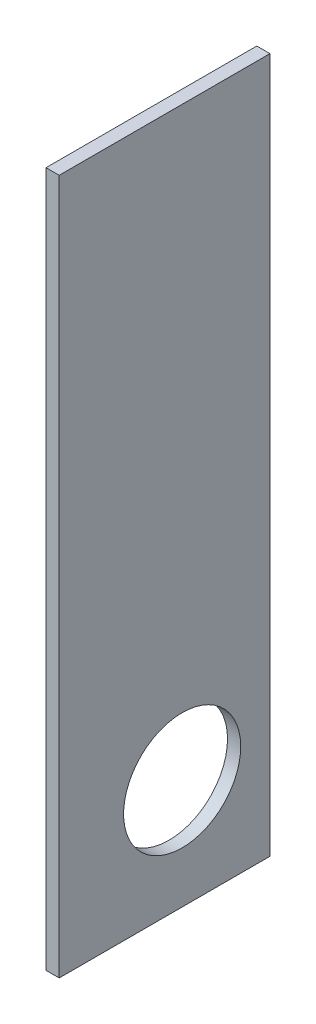
SolidWorks part; units mm, degrees
ref_plane "Front Plane" through (0, 0, 0) normal (0, 0, 1) x (1, 0, 0)
ref_plane "Top Plane" through (0, 0, 0) normal (0, 1, 0) x (1, 0, 0)
ref_plane "Right Plane" through (0, 0, 0) normal (1, 0, 0) x (0, 0, -1)
sketch "Sketch1" plane through (0, 0, 0) normal (1, 0, 0) x (0, 0, -1)
  line L1 (20.3921, -892.2196) -> (-267.6079, -892.2196)
  line L2 (20.3921, -892.2196) -> (20.3921, 57.7804)
  line L3 (20.3921, 57.7804) -> (-267.6079, 57.7804)
  line L4 (-267.6079, -892.2196) -> (-267.6079, 57.7804)
  line L5 (20.3921, -892.2196) -> (-267.6079, 57.7804) construction
  line L6 (20.3921, 57.7804) -> (-267.6079, -892.2196) construction
  point P0 (-123.6079, -417.2196)
  dimension "D1" = 288
  dimension "D2" = 950
extrude "Boss-Extrude1" add sketch "Sketch1" along normal blind 18
sketch "Sketch2" plane through (18, 0, 0) normal (1, 0, 0) x (0, 0, -1)
  line L1 (-267.6079, -892.2196) -> (20.3921, -892.2196) construction
  line L2 (20.3921, -892.2196) -> (20.3921, 57.7804) construction
  circle A0 centre (-99.6079, -742.2196) radius 80
  dimension "D2" = 160
  dimension "D1" = 120
  dimension "D3" = 150
extrude "Cut-Extrude1" cut sketch "Sketch2" against normal through all
equation "\"H_POLKI\"=950"
equation "\"D2@Sketch1\"=\"H_POLKI\""
equation "\"DSP_WIDTH\"=18"
equation "\"D1@Boss-Extrude1\"=\"DSP_WIDTH\""
